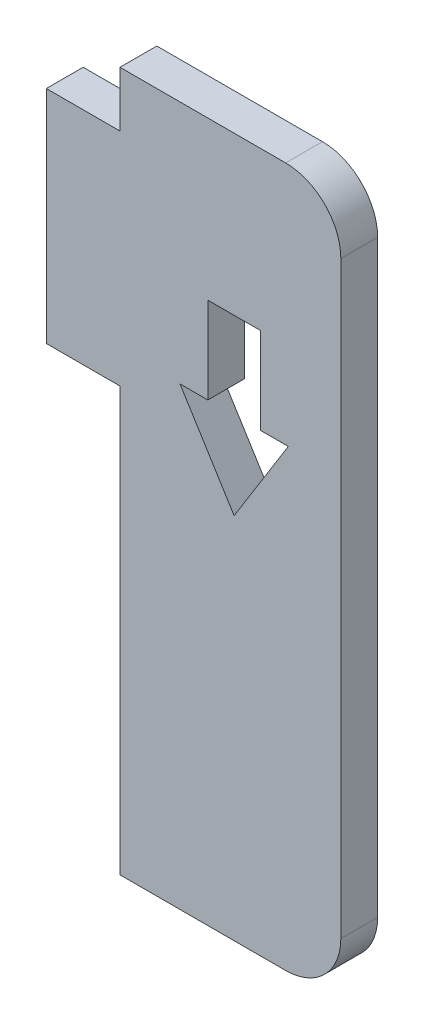
SolidWorks part; units mm, degrees
material "ﾊﾞﾙｻ"
ref_plane "正面" through (0, 0, 0) normal (0, 0, 1) x (1, 0, 0)
ref_plane "平面" through (0, 0, 0) normal (0, 1, 0) x (1, 0, 0)
ref_plane "右側面" through (0, 0, 0) normal (1, 0, 0) x (0, 0, -1)
sketch "ｽｹｯﾁ1" plane through (0, 0, 0) normal (0, 0, 1) x (1, 0, 0)
  line L0 (0, 0) -> (0, -12)
  line L1 (0, -12) -> (4, -12)
  line L2 (4, -12) -> (4, -35)
  line L3 (4, -35) -> (16, -35)
  line L4 (16, -35) -> (16, 3)
  line L5 (16, 3) -> (4, 3)
  line L6 (4, 3) -> (4, 0)
  line L7 (4, 0) -> (0, 0)
  line L8 (4, -25) -> (16, -25)
  dimension "D1" = 12
  dimension "D2" = 4
  dimension "D3" = 3
  dimension "D4" = 12
  dimension "D5" = 23
  dimension "D6" = 13
extrude "ﾎﾞｽ - 押し出し1" add sketch "ｽｹｯﾁ1" along normal blind 2 contours L2 L8 L4 L5 L6 L7 L0 L1 | L8 L2 L3 L4
sketch "ｽｹｯﾁ2" plane through (0, 0, 2) normal (0, 0, 1) x (1, 0, 0)
  line L0 (10.2029, -4.1401) -> (10.2029, -16.3526) construction
  line L1 (11.6328, -5.5701) -> (8.7729, -5.5701)
  line L2 (8.7729, -5.5701) -> (8.7729, -10.2686)
  line L3 (8.7729, -10.2686) -> (7.2608, -10.2686)
  line L4 (7.2608, -10.2686) -> (10.2029, -15)
  line L5 (13.145, -10.2686) -> (10.2029, -15)
  line L6 (11.6328, -10.2686) -> (13.145, -10.2686)
  line L7 (11.6328, -5.5701) -> (11.6328, -10.2686)
  line L8 (16, -35) -> (16, 3) construction
  line L9 (16, 3) -> (4, 3) construction
  point P10 (10.2029, -5.5701)
  dimension "D1" = 2.855
  dimension "D2" = 4.3672
  dimension "D3" = 5.7971
  dimension "D4" = 8.5701
  dimension "D5" = 13.2686
  dimension "D6" = 18
extrude "ｶｯﾄ - 押し出し1" cut sketch "ｽｹｯﾁ2" against normal blind 2
fillet "ﾌｨﾚｯﾄ1" radius 3 2 edges at (16, -35, 1) (16, 3, 1)
